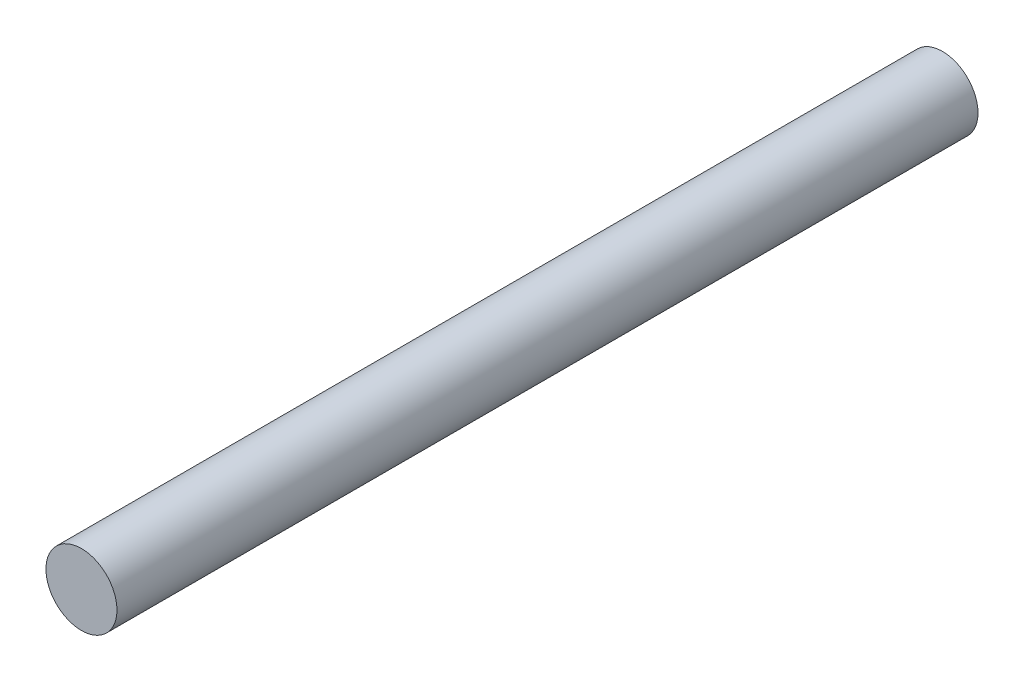
SolidWorks part; units mm, degrees
ref_plane "Přední rovina" through (0, 0, 0) normal (0, 0, 1) x (1, 0, 0)
ref_plane "Horní rovina" through (0, 0, 0) normal (0, 1, 0) x (1, 0, 0)
ref_plane "Pravá rovina" through (0, 0, 0) normal (1, 0, 0) x (0, 0, -1)
sketch "Skica1" plane through (0, 0, 0) normal (0, 0, 1) x (1, 0, 0)
  circle A0 centre (0, 0) radius 1.65
  dimension "D1" = 3.3
extrude "Přidat vysunutím1" add sketch "Skica1" along normal blind 40
